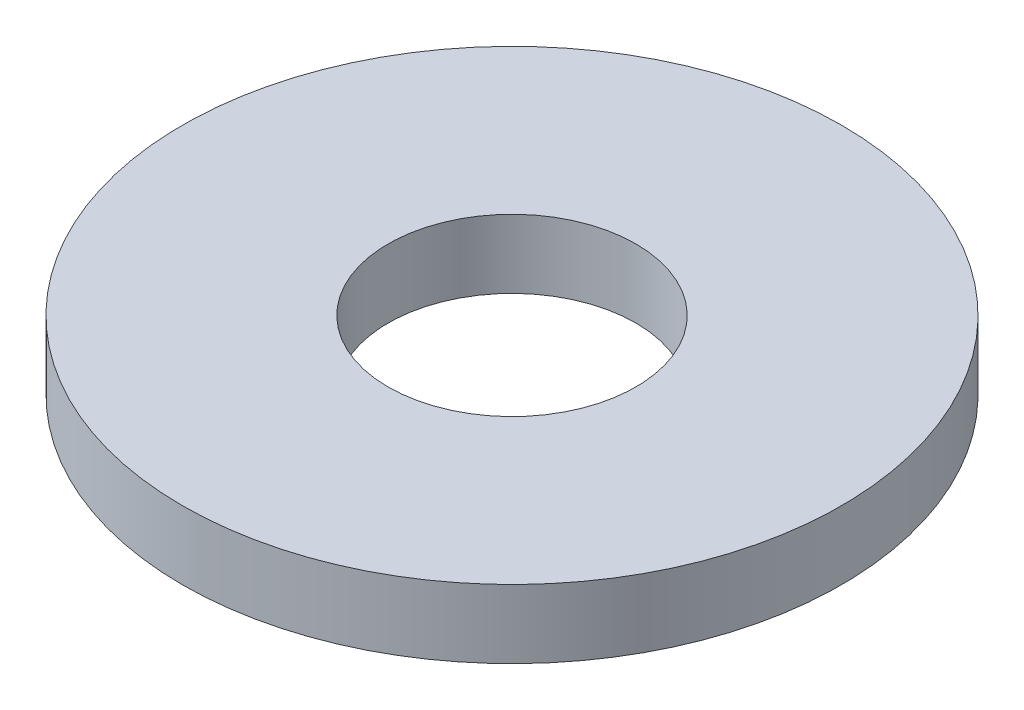
SolidWorks part; units mm, degrees
material "AISI 316 Annealed Stainless Steel Bar (SS)"
ref_plane "Front Plane" through (0, 0, 0) normal (0, 0, 1) x (1, 0, 0)
ref_plane "Top Plane" through (0, 0, 0) normal (0, 1, 0) x (1, 0, 0)
ref_plane "Right Plane" through (0, 0, 0) normal (1, 0, 0) x (0, 0, -1)
sketch "Sketch1" plane through (0, 0, 0) normal (0, 1, 0) x (1, 0, 0)
  circle A0 centre (0, 0) radius 4.7625
  dimension "OD" = 9.525
extrude "Boss-Extrude1" add sketch "Sketch1" along normal blind 0.9906
sketch "Sketch5" plane through (0, 0.9906, 0) normal (0, 1, 0) x (-1, 0, 0)
  circle A0 centre (0, 0) radius 1.7907
  dimension "ID" = 3.5814
extrude "Cut-Extrude1" cut sketch "Sketch5" against normal through all
